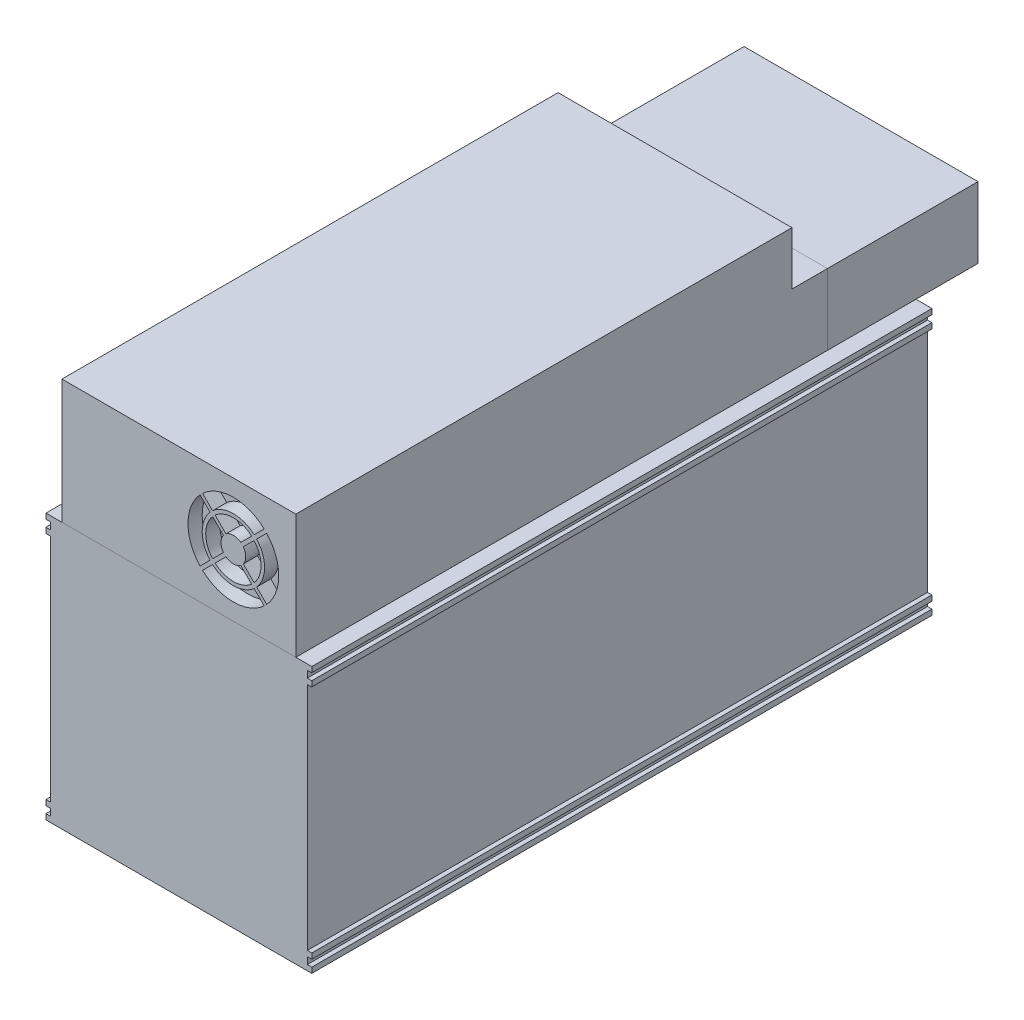
SolidWorks part; units mm, degrees
ref_plane "Front Plane" through (0, 0, 0) normal (0, 0, 1) x (1, 0, 0)
ref_plane "Top Plane" through (0, 0, 0) normal (0, 1, 0) x (1, 0, 0)
ref_plane "Right Plane" through (0, 0, 0) normal (1, 0, 0) x (0, 0, -1)
sketch "Sketch1" plane through (0, 0, 0) normal (0, 0, 1) x (1, 0, 0)
  line L1 (-75, 75) -> (75, 75)
  line L2 (-75, 75) -> (-75, -75)
  line L3 (-75, -75) -> (75, -75)
  line L4 (75, 75) -> (75, -75)
  line L5 (-75, 75) -> (75, -75) construction
  line L6 (-75, -75) -> (75, 75) construction
  point P0 (0, 0)
  dimension "D1" = 150
  dimension "D2" = 150
extrude "Boss-Extrude1" add sketch "Sketch1" along normal blind 350
sketch "Sketch2" plane through (0, 0, 350) normal (0, 0, 1) x (1, 0, 0)
  line L0 (0, 75) -> (0, 145) construction
  line L1 (-66, 75) -> (66, 75)
  line L2 (-66, 75) -> (-66, 145)
  line L3 (-66, 145) -> (66, 145)
  line L4 (66, 75) -> (66, 145)
  line L5 (75, -75) -> (75, 75) construction
  dimension "D1" = 66
  dimension "D2" = 9
  dimension "D3" = 70
extrude "Boss-Extrude2" add sketch "Sketch2" against normal blind 300 separate body
sketch "Sketch3" plane through (-66, 0, 0) normal (-1, 0, 0) x (0, 0, 1)
  line L1 (50, 145) -> (70, 145)
  line L2 (50, 145) -> (50, 115)
  line L3 (50, 115) -> (70, 115)
  line L4 (70, 145) -> (70, 115)
  dimension "D1" = 20
  dimension "D2" = 30
extrude "Cut-Extrude1" cut sketch "Sketch3" against normal blind 300
sketch "Sketch4" plane through (0, 0, 50) normal (0, 0, -1) x (-1, 0, 0)
  line L4 (66, 115) -> (-66, 115)
  line L5 (-66, 115) -> (-66, 75)
  line L6 (-66, 75) -> (66, 75)
  line L7 (66, 75) -> (66, 115)
  line L8 (66, 115) -> (-66, 115)
  line L9 (-66, 115) -> (-66, 75)
  line L10 (-66, 75) -> (66, 75)
  line L11 (66, 75) -> (66, 115)
  dimension "D1" = 0
extrude "Boss-Extrude3" add sketch "Sketch4" along normal blind 85 separate body
sketch "Sketch5" plane through (0, 0, 350) normal (0, 0, 1) x (1, 0, 0)
  line L0 (75, -75) -> (75, 75) construction
  line L1 (77.5, -65) -> (72.5, -65)
  line L2 (77.5, -65) -> (77.5, 65)
  line L3 (77.5, 65) -> (72.5, 65)
  line L4 (72.5, -65) -> (72.5, 65)
  line L5 (77.5, -65) -> (72.5, 65) construction
  line L6 (77.5, 65) -> (72.5, -65) construction
  point P0 (75, 0)
  dimension "D1" = 130
  dimension "D2" = 5
extrude "Cut-Extrude2" cut sketch "Sketch5" against normal blind 448
sketch "Sketch6" plane through (0, 0, 350) normal (0, 0, 1) x (1, 0, 0)
  line L0 (75, 65) -> (75, 75) construction
  line L1 (77.5, 71.9287) -> (72.5, 71.9287)
  line L2 (77.5, 71.9287) -> (77.5, 68.0713)
  line L3 (77.5, 68.0713) -> (72.5, 68.0713)
  line L4 (72.5, 71.9287) -> (72.5, 68.0713)
  line L5 (77.5, 71.9287) -> (72.5, 68.0713) construction
  line L6 (77.5, 68.0713) -> (72.5, 71.9287) construction
  line L7 (72.5, 65) -> (72.5, -65) construction
  point P0 (75, 70)
  dimension "D1" = 0
extrude "Cut-Extrude3" cut sketch "Sketch6" against normal blind 448
mirror "Mirror1" about plane through (0, 0, 0) normal (0, 1, 0) of "Cut-Extrude3"
mirror "Mirror2" about plane through (0, 0, 0) normal (1, 0, 0) of "Mirror1", "Cut-Extrude2", "Cut-Extrude3"
sketch "Sketch7" plane through (0, 0, 350) normal (0, 0, 1) x (1, 0, 0)
  line L0 (30.7427, 110) -> (30.7427, 137.3974) construction
  line L1 (34.9317, 104.3968) -> (41.0525, 98.2759)
  line L2 (36.3459, 105.811) -> (42.4667, 99.6902)
  line L3 (36.3459, 114.189) -> (42.4667, 120.3098)
  line L4 (43.8835, 121.7266) -> (49.5467, 127.3898)
  line L5 (34.9317, 115.6032) -> (41.0525, 121.7241)
  line L6 (42.4693, 123.1409) -> (48.1325, 128.804)
  line L7 (43.8835, 98.2734) -> (49.5467, 92.6102)
  line L8 (42.4693, 96.8591) -> (48.1325, 91.196)
  line L9 (25.1394, 105.811) -> (19.0186, 99.6902)
  line L10 (26.5537, 104.3968) -> (20.4328, 98.2759)
  line L11 (19.016, 96.8591) -> (13.3529, 91.196)
  line L12 (17.6018, 98.2734) -> (11.9387, 92.6102)
  line L13 (26.5537, 115.6032) -> (20.4328, 121.7241)
  line L14 (25.1394, 114.189) -> (19.0186, 120.3098)
  line L15 (17.6018, 121.7266) -> (11.9387, 127.3898)
  line L16 (19.016, 123.1409) -> (13.3529, 128.804)
  circle A0 centre (30.7427, 110) radius 27.3974
  arc A1 (48.1325, 128.804) -> (13.3529, 128.804) centre (30.7427, 110) ccw
  arc A2 (41.0525, 121.7241) -> (20.4328, 121.7241) centre (30.7427, 110) ccw
  arc A3 (42.4693, 123.1409) -> (19.016, 123.1409) centre (30.7427, 110) ccw
  arc A4 (34.9317, 115.6032) -> (26.5537, 115.6032) centre (30.7427, 110) ccw
  circle A5 centre (30.7427, 110) radius 15.6124 construction
  circle A6 centre (30.7427, 110) radius 17.6124 construction
  arc A7 (36.3459, 105.811) -> (36.3459, 114.189) centre (30.7427, 110) ccw
  arc A8 (42.4667, 99.6902) -> (42.4667, 120.3098) centre (30.7427, 110) ccw
  arc A9 (43.8835, 98.2734) -> (43.8835, 121.7266) centre (30.7427, 110) ccw
  arc A10 (20.4328, 98.2759) -> (41.0525, 98.2759) centre (30.7427, 110) ccw
  arc A11 (19.016, 96.8591) -> (42.4693, 96.8591) centre (30.7427, 110) ccw
  arc A12 (26.5537, 104.3968) -> (34.9317, 104.3968) centre (30.7427, 110) ccw
  arc A13 (25.1394, 114.189) -> (25.1394, 105.811) centre (30.7427, 110) ccw
  arc A14 (19.0186, 120.3098) -> (19.0186, 99.6902) centre (30.7427, 110) ccw
  arc A15 (17.6018, 121.7266) -> (17.6018, 98.2734) centre (30.7427, 110) ccw
  circle A16 centre (30.7427, 110) radius 25.6124 construction
  arc A17 (11.9387, 127.3898) -> (11.9387, 92.6102) centre (30.7427, 110) ccw
  arc A18 (13.3529, 91.196) -> (48.1325, 91.196) centre (30.7427, 110) ccw
  arc A19 (49.5467, 92.6102) -> (49.5467, 127.3898) centre (30.7427, 110) ccw
  dimension "D3" = 4
  dimension "D1" = 10
  dimension "D2" = 2
extrude "Cut-Extrude5" cut sketch "Sketch7" against normal blind 8 contours L15 A17 L12 A15 | A3 L6 A1 L16 | L7 A19 L4 A9 | L11 A18 L8 A11 | A12 L10 A10 L1 | L14 A14 L9 A13 | A4 L5 A2 L13 | L2 A8 L3 A7 | A0
